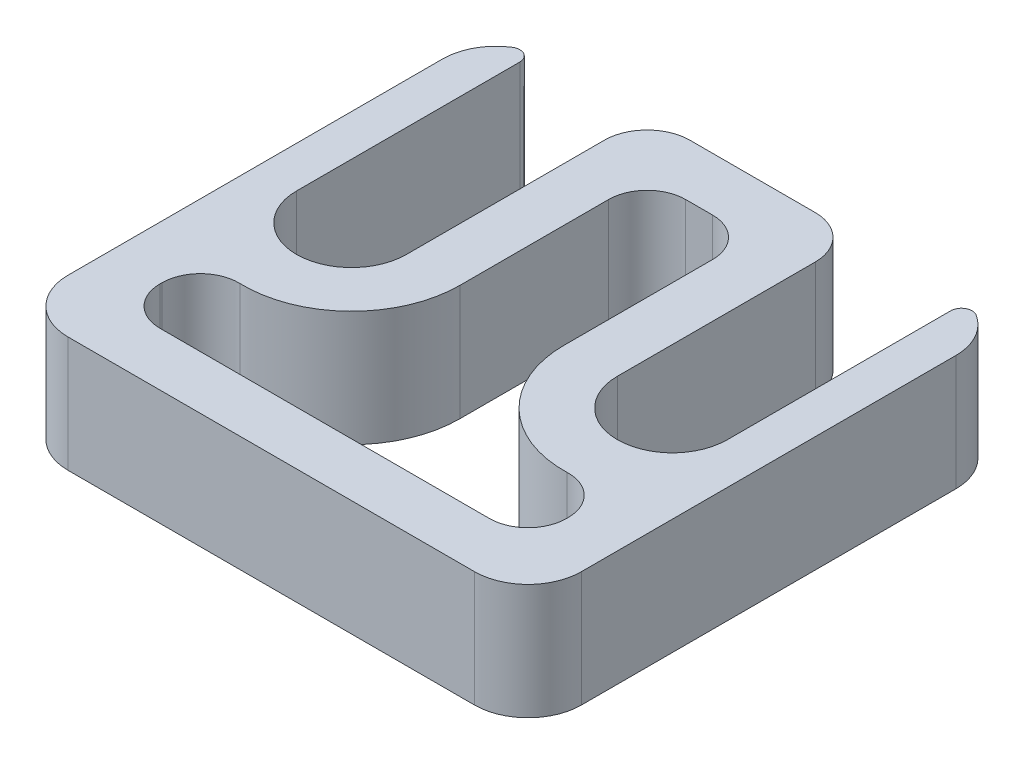
SolidWorks part; units mm, degrees
material "6061-T6 (SS)"
ref_plane "Front Plane" through (0, 0, 0) normal (0, 0, 1) x (1, 0, 0)
ref_plane "Top Plane" through (0, 0, 0) normal (0, 1, 0) x (1, 0, 0)
ref_plane "Right Plane" through (0, 0, 0) normal (1, 0, 0) x (0, 0, -1)
sketch "Sketch1" plane through (0, 546.1, 533.9386) normal (0, -1, 0) x (1, 0, 0)
  line L5 (21.5011, -242.3466) -> (21.5011, -256.6341)
  line L16 (28.0289, -242.3466) -> (28.0289, -256.5504)
  line L17 (27.305, -256.6341) -> (3.175, -256.6341) construction
  line L23 (8.9789, -242.3466) -> (8.9789, -256.6341)
  line L24 (2.4511, -242.3466) -> (2.4511, -256.5504)
  line L25 (0, -231.2341) -> (0, -253.4591)
  line L26 (27.305, -228.0591) -> (3.175, -228.0591)
  line L27 (30.48, -253.4591) -> (30.48, -231.2341)
  line L28 (3.175, -256.6341) -> (27.305, -256.6341)
  line L29 (0, -231.2341) -> (0, -253.4591)
  line L30 (27.305, -228.0591) -> (3.175, -228.0591)
  line L31 (30.48, -253.4591) -> (30.48, -231.2341)
  line L32 (8.9789, -256.6341) -> (21.5011, -256.6341)
  circle A9 centre (5.715, -242.3466) radius 3.2639 construction
  circle A10 centre (24.765, -242.3466) radius 3.2639 construction
  arc A11 (8.9789, -242.3466) -> (2.4511, -242.3466) centre (5.715, -242.3466) ccw
  arc A12 (28.0289, -242.3466) -> (21.5011, -242.3466) centre (24.765, -242.3466) ccw
  arc A13 (0, -253.4591) -> (3.175, -256.6341) centre (3.175, -253.4591) ccw
  arc A14 (3.175, -228.0591) -> (0, -231.2341) centre (3.175, -231.2341) ccw
  arc A15 (30.48, -231.2341) -> (27.305, -228.0591) centre (27.305, -231.2341) ccw
  arc A16 (27.305, -256.6341) -> (30.48, -253.4591) centre (27.305, -253.4591) ccw
  arc A17 (0, -253.4591) -> (2.4511, -256.5504) centre (3.175, -253.4591) ccw
  arc A18 (3.175, -228.0591) -> (0, -231.2341) centre (3.175, -231.2341) ccw
  arc A19 (30.48, -231.2341) -> (27.305, -228.0591) centre (27.305, -231.2341) ccw
  arc A20 (28.0289, -256.5504) -> (30.48, -253.4591) centre (27.305, -253.4591) ccw
  dimension "D1" = 0
extrude "Boss-Extrude1" add sketch "Sketch1" against normal blind 6.858
fillet "Fillet1" radius 2.54 2 edges at (21.5011, 549.529, 277.3045) (8.9789, 549.529, 277.3045)
fillet "Fillet2" radius 0.635 2 edges at (28.0289, 549.529, 277.3881) (2.4511, 549.529, 277.3881)
sketch "Sketch2" plane through (0, 546.1, 0) normal (0, -1, 0) x (1, 0, 0)
  line L27 (27.305, 297.5087) -> (27.305, 297.5087)
  line L28 (27.305, 297.5087) -> (27.305, 302.7045)
  line L29 (27.305, 302.7045) -> (3.175, 302.7045)
  line L30 (3.175, 302.7045) -> (3.175, 297.5087)
  line L31 (3.175, 297.5087) -> (3.175, 297.5087)
  line L32 (12.1539, 291.592) -> (12.1539, 280.4795)
  line L33 (12.1539, 280.4795) -> (18.3261, 280.4795)
  line L34 (18.3261, 280.4795) -> (18.3261, 291.592)
  line L35 (28.0289, 291.592) -> (28.0289, 278.3336)
  line L36 (30.48, 280.4795) -> (30.48, 302.7045)
  line L37 (27.305, 305.8795) -> (3.175, 305.8795)
  line L38 (0, 302.7045) -> (0, 280.4795)
  line L39 (2.4511, 278.3336) -> (2.4511, 291.592)
  line L40 (8.9789, 291.592) -> (8.9789, 279.8445)
  line L41 (11.5189, 277.3045) -> (18.9611, 277.3045)
  line L42 (21.5011, 279.8445) -> (21.5011, 291.592)
  line L43 (28.0289, 291.592) -> (28.0289, 278.3336)
  line L44 (30.48, 280.4795) -> (30.48, 302.7045)
  line L45 (27.305, 305.8795) -> (3.175, 305.8795)
  line L46 (0, 302.7045) -> (0, 280.4795)
  line L47 (2.4511, 278.3336) -> (2.4511, 291.592)
  line L48 (8.9789, 291.592) -> (8.9789, 279.8445)
  line L49 (11.5189, 277.3045) -> (18.9611, 277.3045)
  line L50 (21.5011, 279.8445) -> (21.5011, 291.592)
  arc A31 (27.305, 297.5087) -> (27.305, 297.5087) centre (27.305, 297.5087) ccw
  arc A32 (27.305, 297.5087) -> (27.305, 297.5087) centre (27.305, 297.5087) ccw
  arc A33 (27.305, 302.7045) -> (27.305, 302.7045) centre (27.305, 302.7045) ccw
  arc A34 (3.175, 302.7045) -> (3.175, 302.7045) centre (3.175, 302.7045) ccw
  arc A35 (3.175, 297.5087) -> (3.175, 297.5087) centre (3.175, 297.5087) ccw
  arc A36 (3.175, 297.5087) -> (3.175, 297.5087) centre (3.175, 297.5087) ccw
  arc A37 (12.1539, 291.592) -> (3.175, 297.5087) centre (5.715, 291.592) ccw
  arc A38 (12.1539, 280.4795) -> (12.1539, 280.4795) centre (12.1539, 280.4795) ccw
  arc A39 (18.3261, 280.4795) -> (18.3261, 280.4795) centre (18.3261, 280.4795) ccw
  arc A40 (27.305, 297.5087) -> (18.3261, 291.592) centre (24.765, 291.592) ccw
  arc A41 (28.0289, 278.3336) -> (29.0036, 277.7971) centre (28.6639, 278.3336) ccw
  arc A42 (29.0036, 277.7971) -> (30.48, 280.4795) centre (27.305, 280.4795) ccw
  arc A43 (30.48, 302.7045) -> (27.305, 305.8795) centre (27.305, 302.7045) ccw
  arc A44 (3.175, 305.8795) -> (0, 302.7045) centre (3.175, 302.7045) ccw
  arc A45 (0, 280.4795) -> (1.4764, 277.7971) centre (3.175, 280.4795) ccw
  arc A46 (1.4764, 277.7971) -> (2.4511, 278.3336) centre (1.8161, 278.3336) ccw
  arc A47 (8.9789, 291.592) -> (2.4511, 291.592) centre (5.715, 291.592) ccw
  arc A48 (8.9789, 279.8445) -> (11.5189, 277.3045) centre (11.5189, 279.8445) ccw
  arc A49 (18.9611, 277.3045) -> (21.5011, 279.8445) centre (18.9611, 279.8445) ccw
  arc A50 (28.0289, 291.592) -> (21.5011, 291.592) centre (24.765, 291.592) ccw
  arc A51 (28.0289, 278.3336) -> (29.0036, 277.7971) centre (28.6639, 278.3336) ccw
  arc A52 (29.0036, 277.7971) -> (30.48, 280.4795) centre (27.305, 280.4795) ccw
  arc A53 (30.48, 302.7045) -> (27.305, 305.8795) centre (27.305, 302.7045) ccw
  arc A54 (3.175, 305.8795) -> (0, 302.7045) centre (3.175, 302.7045) ccw
  arc A55 (0, 280.4795) -> (1.4764, 277.7971) centre (3.175, 280.4795) ccw
  arc A56 (1.4764, 277.7971) -> (2.4511, 278.3336) centre (1.8161, 278.3336) ccw
  arc A57 (8.9789, 291.592) -> (2.4511, 291.592) centre (5.715, 291.592) ccw
  arc A58 (8.9789, 279.8445) -> (11.5189, 277.3045) centre (11.5189, 279.8445) ccw
  arc A59 (18.9611, 277.3045) -> (21.5011, 279.8445) centre (18.9611, 279.8445) ccw
  arc A60 (28.0289, 291.592) -> (21.5011, 291.592) centre (24.765, 291.592) ccw
  dimension "D1" = 0
  dimension "D2" = 3.175
extrude "Cut-Extrude1" cut sketch "Sketch2" against normal through all both and the other way through all contours A40 L28 L29 L30 A37 L32 L33 L34 | L43 A51 A52 L44 A53 L45 A54 L46 A55 A56 L47 A57 L48 A58 L49 A59 L50 A60
fillet "Fillet3" radius 2.286 6 edges at (18.3261, 549.529, 280.4795) (27.305, 549.529, 297.5087) (27.305, 549.529, 302.7045) (3.175, 549.529, 302.7045) (3.175, 549.529, 297.5087) (12.1539, 549.529, 280.4795)
